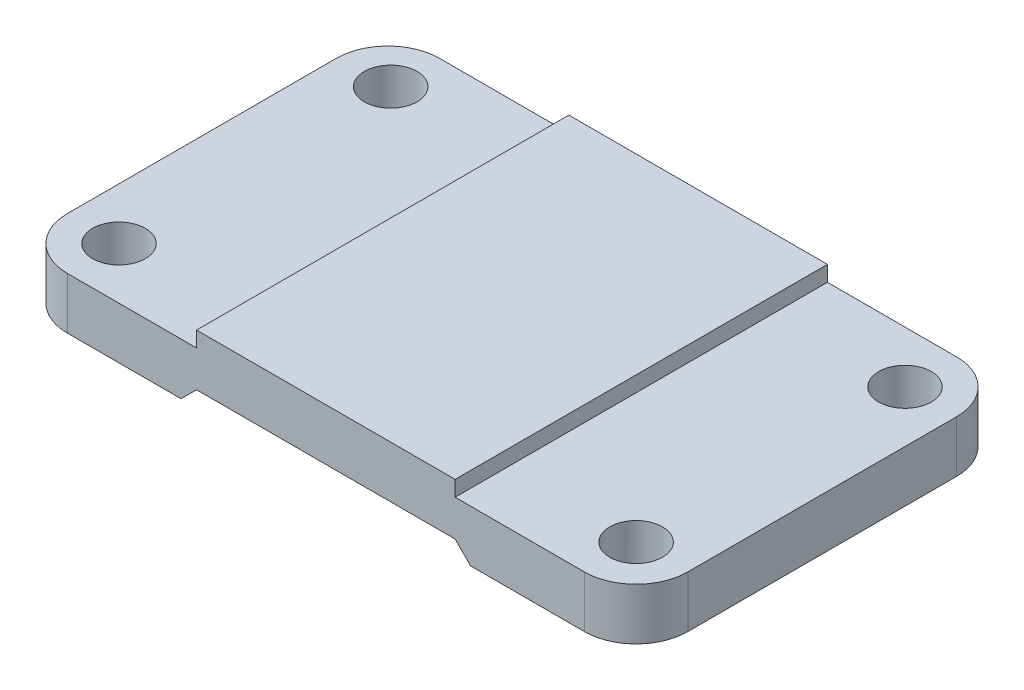
SolidWorks part; units mm, degrees
ref_plane "Front Plane" through (0, 0, 0) normal (0, 0, 1) x (1, 0, 0)
ref_plane "Top Plane" through (0, 0, 0) normal (0, 1, 0) x (1, 0, 0)
ref_plane "Right Plane" through (0, 0, 0) normal (1, 0, 0) x (0, 0, -1)
sketch "Sketch1" plane through (0, 0, 0) normal (0, 1, 0) x (1, 0, 0)
  line L2 (-60, -36) -> (60, -36)
  line L3 (-60, -36) -> (-60, 36)
  line L4 (-60, 36) -> (60, 36)
  line L5 (60, -36) -> (60, 36)
  line L6 (-60, -36) -> (60, 36) construction
  line L7 (-60, 36) -> (60, -36) construction
  point P1 (0, 0)
  dimension "D1" = 120
  dimension "D2" = 72
extrude "Boss-Extrude1" add sketch "Sketch1" along normal blind 10
fillet "Fillet1" radius 10 4 edges at (-60, 5, 36) (-60, 5, -36) (60, 5, -36) (60, 5, 36)
hole_wizard "M12 Tapped Hole1" positions "Sketch2" profile "Sketch3" tap size "M12" standard "DIN" end condition up to next
sketch "Sketch2" plane through (0, 10, 0) normal (0, 1, 0) x (1, 0, 0)
  point P0 (0, 43.3711)
  point P2 (50, -26)
  point P5 (50, 26)
  point P8 (-50, 26.5405)
  point P17 (-50, -26)
sketch "Sketch3" plane through (0, 10, -43.3711) normal (1, 0, 0) x (0, 0, 1)
  line L0 (0, 0) -> (0, 10)
  line L1 (0, 10) -> (5.1, 10)
  line L2 (5.1, 10) -> (5.1, 0)
  line L5 (5.1, 0) -> (0, 0)
  line L11 (0, -6.35) -> (0, 107.95) construction
  dimension "Thru Tap Drill Dia." = 10.2
  dimension "Thru Tap Drill Depth" = 10
cosmetic thread "Hole Thread1" parameters "D2"=12
cosmetic thread "Hole Thread2" parameters "D2"=12
cosmetic thread "Hole Thread3" parameters "D2"=12
cosmetic thread "Hole Thread4" parameters "D2"=12
sketch "Sketch4" plane through (0, 10, 0) normal (0, 1, 0) x (1, 0, 0)
  line L0 (50, 36) -> (-50, 36) construction
  line L1 (-25, -36) -> (25, -36)
  line L2 (-25, -36) -> (-25, 36)
  line L3 (-25, 36) -> (25, 36)
  line L4 (25, -36) -> (25, 36)
  line L5 (-25, -36) -> (25, 36) construction
  line L6 (-25, 36) -> (25, -36) construction
  point P0 (0, 0)
  dimension "D1" = 50
extrude "Boss-Extrude2" add sketch "Sketch4" along normal blind 3
sketch "Sketch5" plane through (0, 0, 36) normal (0, 0, 1) x (1, 0, 0)
  line L0 (-28, 0) -> (-25, 3)
  line L2 (-50, 0) -> (50, 0) construction
  line L3 (-25, 3) -> (25, 3)
  line L4 (25, 3) -> (28, 0)
  line L5 (-28, 0) -> (28, 0)
  line L6 (0, 2.9237) -> (0, 0) construction
  dimension "D1" = 56
  dimension "D2" = 45
  dimension "D3" = 3
extrude "Cut-Extrude1" cut sketch "Sketch5" against normal through all
